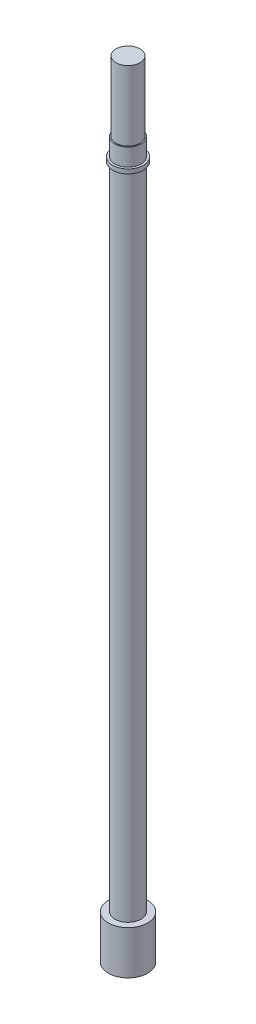
SolidWorks part; units mm, degrees
ref_plane "Спереди" through (0, 0, 0) normal (0, 0, 1) x (1, 0, 0)
ref_plane "Сверху" through (0, 0, 0) normal (0, 1, 0) x (1, 0, 0)
ref_plane "Справа" through (0, 0, 0) normal (1, 0, 0) x (0, 0, -1)
sketch "Sketch2" plane through (0, 0, 0) normal (0, 1, 0) x (1, 0, 0)
  circle A0 centre (0, 0) radius 3
  dimension "D1" = 6
extrude "Boss-Extrude1" add sketch "Sketch2" along normal blind 170
sketch "Sketch3" plane through (0, 0, 0) normal (0, -1, 0) x (1, 0, 0)
  circle A0 centre (0, 0) radius 4.5
  dimension "D1" = 9
extrude "Boss-Extrude2" add sketch "Sketch3" along normal blind 10
sketch "Sketch4" plane through (0, 170, 0) normal (0, 1, 0) x (1, 0, 0)
  circle A0 centre (0, 0) radius 2.75
  dimension "D1" = 5.5
extrude "Cut-Extrude1" cut sketch "Sketch4" against normal blind 16 flip side to cut
sketch "Sketch5" plane through (0, 170, 0) normal (0, 1, 0) x (1, 0, 0)
  circle A0 centre (0, 0) radius 3.5
  dimension "D1" = 7
extrude "Boss-Extrude3" add sketch "Sketch5" along normal blind 1 from offset 21
